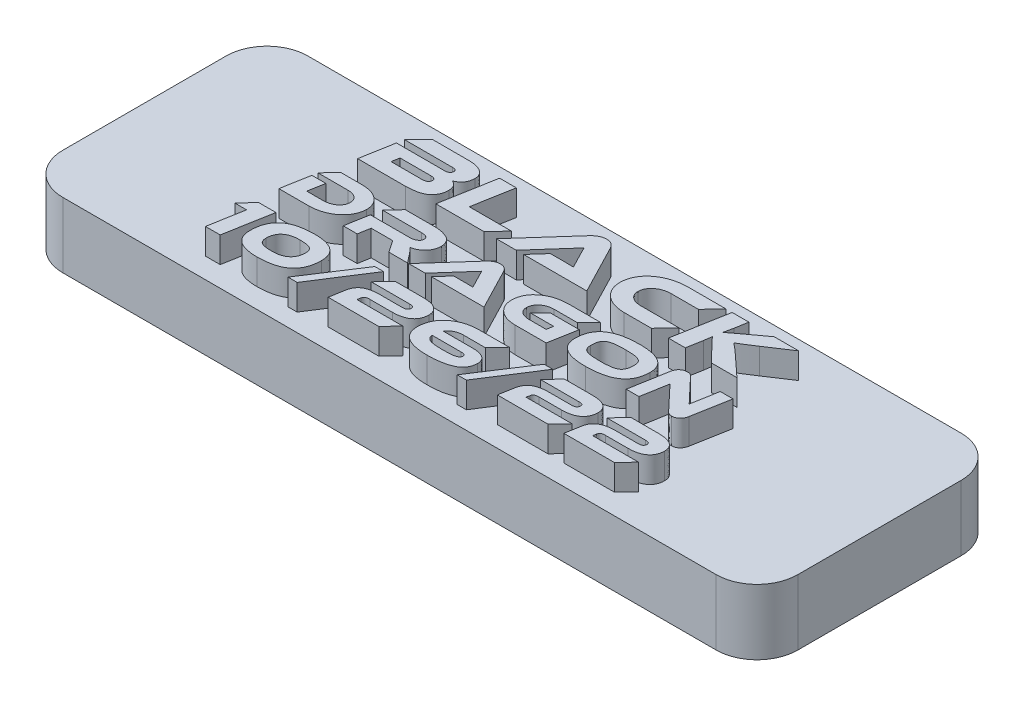
SolidWorks part; units mm, degrees
ref_plane "Front Plane" through (0, 0, 0) normal (0, 0, 1) x (1, 0, 0)
ref_plane "Top Plane" through (0, 0, 0) normal (0, 1, 0) x (1, 0, 0)
ref_plane "Right Plane" through (0, 0, 0) normal (1, 0, 0) x (0, 0, -1)
sketch "Sketch1" plane through (0, 0, 0) normal (0, 1, 0) x (1, 0, 0)
  line L1 (-28.575, 9.525) -> (28.575, 9.525)
  line L2 (-28.575, 9.525) -> (-28.575, -9.525)
  line L3 (-28.575, -9.525) -> (28.575, -9.525)
  line L4 (28.575, 9.525) -> (28.575, -9.525)
  line L5 (-28.575, 9.525) -> (28.575, -9.525) construction
  line L6 (-28.575, -9.525) -> (28.575, 9.525) construction
  point P0 (0, 0)
  dimension "D1" = 57.15
  dimension "D2" = 19.05
extrude "Boss-Extrude1" add sketch "Sketch1" along normal up to surface (5.08 mm away)
fillet "Fillet1" radius 3.175 4 edges at (-28.575, 2.54, 9.525) (-28.575, 2.54, -9.525) (28.575, 2.54, 9.525) (28.575, 2.54, -9.525)
sketch "Sketch3" plane through (0, 5.08, 0) normal (0, 1, 0) x (1, 0, 0)
  line L0 (28.575, -7.9375) -> (-28.575, -7.9375) construction
  line L1 (28.575, -6.35) -> (28.575, 6.35) construction
  line L2 (-28.575, 6.35) -> (-28.575, -6.35) construction
  line L3 (28.575, 2.54) -> (-28.575, 2.54) construction
  line L4 (-28.575, -2.54) -> (28.575, -2.54) construction
  line L5 (-25.4, -9.525) -> (25.4, -9.525) construction
  line L6 (25.4, 9.525) -> (-25.4, 9.525) construction
  line L7 (28.575, 2.54) -> (28.575, -2.54) construction
  text T0 "Black" font "Ethnocentric Rg" height in points 16
  text T1 "10/26/22" font "Ethnocentric Rg" height in points 14
  text T2 "dragon" font "Ethnocentric Rg" height 3.5
  point P11 (28.575, 0)
  point P13 (28.575, 0)
  dimension "D1" = 1.5875
  dimension "D2" = 5.08
extrude "Boss-Extrude2" add sketch "Sketch3" along normal blind 2
sketch "Sketch4" plane through (0, 0, 0) normal (0, -1, 0) x (1, 0, 0)
  line L0 (25.4, 0) -> (-25.4, 0) construction
  circle A0 centre (-25.4, 0) radius 0.9
  circle A1 centre (25.4, 0) radius 0.9
  point P3 (0, 0)
  dimension "D2" = 1.8
  dimension "D1" = 50.8
extrude "Cut-Extrude1" cut sketch "Sketch4" against normal blind 4
